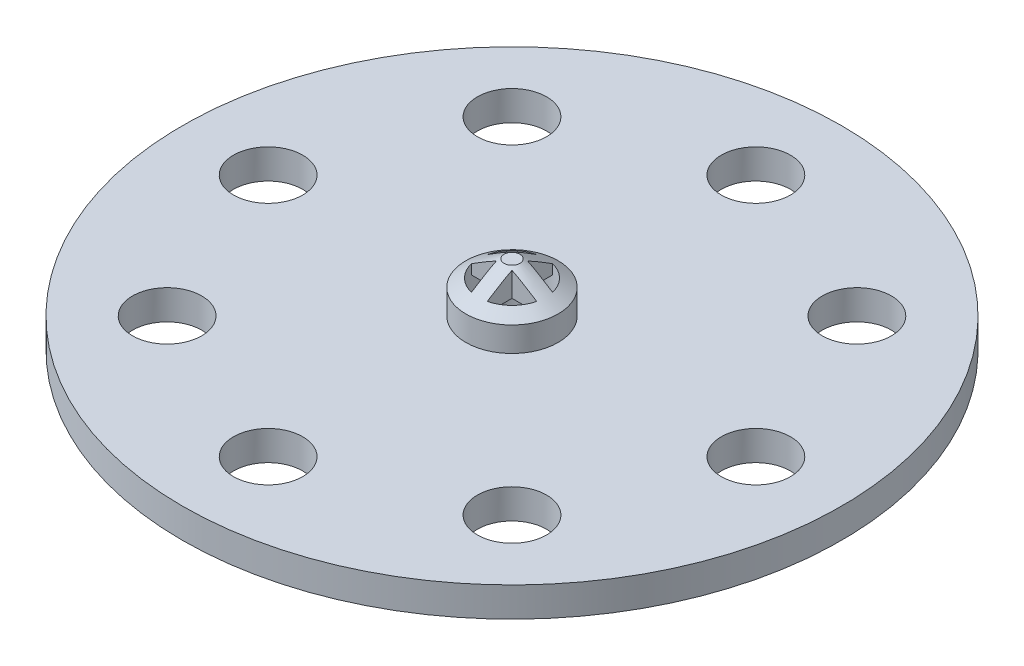
SolidWorks part; units mm, degrees
material "1060 Alloy"
ref_plane "Front Plane" through (0, 0, 0) normal (0, 0, 1) x (1, 0, 0)
ref_plane "Top Plane" through (0, 0, 0) normal (0, 1, 0) x (1, 0, 0)
ref_plane "Right Plane" through (0, 0, 0) normal (1, 0, 0) x (0, 0, -1)
sketch "Sketch1" plane through (0, 0, 0) normal (0, 1, 0) x (1, 0, 0)
  circle A0 centre (0, 0) radius 25
  dimension "D1" = 50
extrude "Boss-Extrude1" add sketch "Sketch1" along normal blind 3.5 contours A0
sketch "Sketch3" plane through (0, 3.5, 0) normal (0, 1, 0) x (1, 0, 0)
  circle A0 centre (0, 0) radius 8.75
  dimension "D1" = 17.5
extrude "Boss-Extrude2" add sketch "Sketch3" along normal blind 4
sketch "Sketch4" plane through (0, 3.5, 0) normal (0, 1, 0) x (1, 0, 0)
  circle A0 centre (0, 18.5) radius 2.625
  circle A1 centre (13.0815, 13.0815) radius 2.625
  circle A2 centre (18.5, 0) radius 2.625
  circle A3 centre (13.0815, -13.0815) radius 2.625
  circle A4 centre (0, -18.5) radius 2.625
  circle A5 centre (-13.0815, -13.0815) radius 2.625
  circle A6 centre (-18.5, 0) radius 2.625
  circle A7 centre (-13.0815, 13.0815) radius 2.625
  point P20 (0, 0)
  dimension "D1" = 5.25
  dimension "D2" = 18.5
  dimension "D3" = 8
extrude "Cut-Extrude1" cut sketch "Sketch4" against normal up to surface (3.5 mm away) up to face at (0, 0, 25)
ref_plane "Plane1" through (0, 13.5, 0) normal (0, 1, 0) x (1, 0, 0)
sketch "Sketch7" plane through (0, 0, 0) normal (0, -1, 0) x (1, 0, 0)
  line L0 (1.9, 1.7007) -> (1.9, -1.7007)
  arc A0 (1.9, 1.7007) -> (1.9, -1.7007) centre (0, 0) ccw
  dimension "D1" = 5.1
  dimension "D2" = 1.9
extrude "Cut-Extrude2" cut sketch "Sketch7" against normal blind 10
sketch "Sketch8" plane through (0, 0, 0) normal (1, 0, 0) x (0, 0, -1)
  line L0 (-2.5, 5) -> (2.5, 5) construction
  line L1 (-2.5, 6) -> (2.5, 6)
  line L2 (-2.5, 4) -> (2.5, 4)
  arc A0 (-2.5, 6) -> (-2.5, 4) centre (-2.5, 5) ccw
  arc A1 (2.5, 4) -> (2.5, 6) centre (2.5, 5) ccw
  point P2 (0, 5)
  dimension "D3" = 5
  dimension "D1" = 5
  dimension "D2" = 2
extrude "Cut-Extrude3" cut sketch "Sketch8" along normal through all both and the other way through all
sketch "Sketch9" plane through (0, 0, 0) normal (0, 0, 1) x (1, 0, 0)
  line L0 (-2.5, 5) -> (2.5, 5) construction
  line L1 (-2.5, 6) -> (2.5, 6)
  line L2 (-2.5, 4) -> (2.5, 4)
  arc A0 (-2.5, 6) -> (-2.5, 4) centre (-2.5, 5) ccw
  arc A1 (2.5, 4) -> (2.5, 6) centre (2.5, 5) ccw
  point P2 (0, 5)
  dimension "D1" = 5
  dimension "D2" = 5
  dimension "D3" = 2
extrude "Cut-Extrude4" cut sketch "Sketch9" against normal through all both and the other way through all
sketch "Sketch11" plane through (0, 3.5, 0) normal (0, 1, 0) x (1, 0, 0)
  circle A0 centre (0, 0) radius 25
extrude "Cut-Extrude5" cut sketch "Sketch11" against normal blind 3
sketch "Sketch12" plane through (0, 0.5, 0) normal (0, 1, 0) x (1, 0, 0)
  line L0 (0.6, 0.6) -> (5, 0.6)
  line L1 (-0.6, -5) -> (0.6, -5)
  line L2 (-0.6, -5) -> (-0.6, -0.6)
  line L3 (-0.6, 5) -> (0.6, 5)
  line L4 (0.6, -5) -> (0.6, -0.6)
  line L5 (-0.6, -5) -> (0.6, 5) construction
  line L6 (-0.6, 5) -> (0.6, -5) construction
  line L7 (-5, -0.6) -> (-0.6, -0.6)
  line L8 (-5, -0.6) -> (-5, 0.6)
  line L9 (-5, 0.6) -> (-0.6, 0.6)
  line L10 (5, -0.6) -> (5, 0.6)
  line L11 (-5, -0.6) -> (5, 0.6) construction
  line L12 (-5, 0.6) -> (5, -0.6) construction
  line L13 (-0.6, 0.6) -> (-0.6, 5)
  line L14 (0.6, -0.6) -> (5, -0.6)
  line L15 (0.6, 0.6) -> (0.6, 5)
  point P0 (0, 0)
  point P5 (0, 0)
  dimension "D1" = 1.2
  dimension "D2" = 10
  dimension "D3" = 1.2
  dimension "D4" = 10
extrude "Boss-Extrude3" add sketch "Sketch12" along normal up to surface (3 mm away) up to face at (-0.325, 3.5, 0)
sketch "Sketch13" plane through (0, 0.5, 0) normal (0, 1, 0) x (1, 0, 0)
  circle A0 centre (0, 0) radius 8.75
  circle A2 centre (0, 0) radius 2.55
  arc A3 (1.9, 1.7007) -> (1.9, -1.7007) centre (0, 0) ccw construction
  circle A4 centre (0, 0) radius 8.75 construction
extrude "Boss-Extrude4" add sketch "Sketch13" along normal up to surface (3 mm away) up to face at (0, 3.5, 8.75)
ref_axis "Axis1" through (0, -5.4813, 0) along (0, 1, 0)
sketch "Sketch15" plane through (0, 0, 0) normal (0, 0, 1) x (1, 0, 0)
  line L0 (0, 13.5) -> (-8.75, 7.5)
  line L1 (0, -5.4813) -> (0, 24.1241) construction
  line L2 (-8.75, 7.5) -> (0, 7.5)
  line L3 (8.75, 7.5) -> (-8.75, 7.5) construction
  line L4 (0, 7.5) -> (0, 13.5)
  dimension "D1" = 6
revolve "Revolve1" add sketch "Sketch15" angle 360 about axis through (0, -5.4813, 0) along (0, 1, 0)
sketch "Sketch16" plane through (0, 0, 0) normal (0, -1, 0) x (1, 0, 0)
  line L0 (1.9, 1.7007) -> (1.9, -1.7007)
  circle A0 centre (0, 0) radius 25
  circle A1 centre (13.0815, 13.0815) radius 2.625
  circle A2 centre (0, 18.5) radius 2.625
  circle A3 centre (-13.0815, 13.0815) radius 2.625
  circle A4 centre (-18.5, 0) radius 2.625
  circle A5 centre (-13.0815, -13.0815) radius 2.625
  circle A6 centre (0, -18.5) radius 2.625
  circle A7 centre (13.0815, -13.0815) radius 2.625
  circle A8 centre (18.5, 0) radius 2.625
  arc A9 (1.9, 1.7007) -> (1.9, -1.7007) centre (0, 0) ccw
extrude "Boss-Extrude5" add sketch "Sketch16" along normal blind 2.5
sketch "Sketch17" plane through (0, 0.5, 0) normal (0, 1, 0) x (1, 0, 0)
  circle A0 centre (0, 0) radius 25
  circle A1 centre (0, 0) radius 8.75
extrude "Cut-Extrude6" cut sketch "Sketch17" against normal blind 0.75
sketch "Sketch18" plane through (0, 0.5, 0) normal (0, -1, 0) x (1, 0, 0)
  line L0 (1.9, 1.7007) -> (1.9, -1.7007)
  arc A0 (1.9, 1.7007) -> (1.9, -1.7007) centre (0, 0) ccw
extrude "Cut-Extrude7" cut sketch "Sketch18" against normal blind 1
sketch "Sketch19" plane through (0, -0.25, 0) normal (0, 1, 0) x (1, 0, 0)
  circle A0 centre (0, 0) radius 8.75
  circle A1 centre (0, 0) radius 3.5
  dimension "D1" = 7
extrude "Cut-Extrude8" cut sketch "Sketch19" along normal blind 20
sketch "Sketch20" plane through (0, 6, 0) normal (0, -1, 0) x (1, 0, 0)
  circle A0 centre (0, 0) radius 6.4154
extrude "Cut-Extrude9" cut sketch "Sketch20" against normal blind 10
sketch "Sketch22" plane through (0, 4, 0) normal (0, 1, 0) x (1, 0, 0)
  circle A0 centre (0, 0) radius 3.5
extrude "Cut-Extrude10" cut sketch "Sketch22" against normal up to surface (0.5 mm away) up to face at (-0.1024, 3.5, 0)
sketch "Sketch23" plane through (0, 0, 0) normal (1, 0, 0) x (0, 0, -1)
  line L0 (3.5, 1.625) -> (0.6, 3.5)
  line L1 (3.5, -0.25) -> (3.5, 3.5) construction
  line L4 (3.5, 1.625) -> (3.5, 3.5)
  line L5 (3.5, 3.5) -> (0.6, 3.5)
revolve "Cut-Revolve3" cut sketch "Sketch23" angle 360 about axis through (0, -5.4813, 0) along (0, 1, 0)
